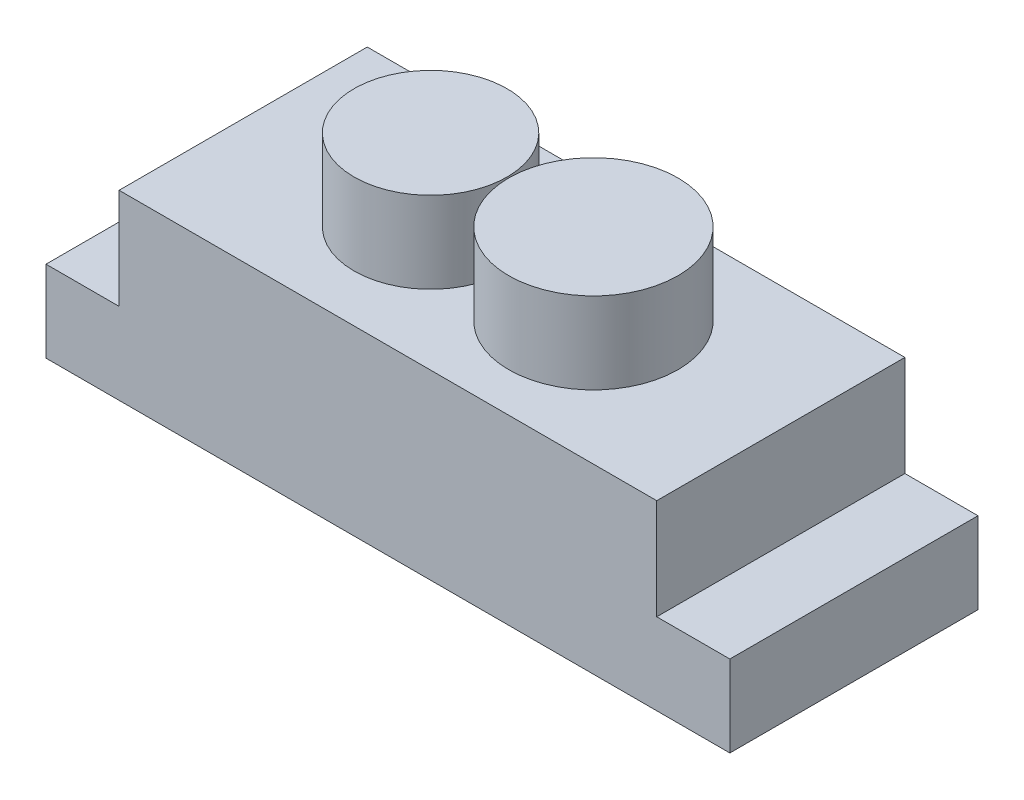
SolidWorks part; units mm, degrees
ref_plane "Front Plane" through (0, 0, 0) normal (0, 0, 1) x (1, 0, 0)
ref_plane "Top Plane" through (0, 0, 0) normal (0, 1, 0) x (1, 0, 0)
ref_plane "Right Plane" through (0, 0, 0) normal (1, 0, 0) x (0, 0, -1)
sketch "Sketch1" plane through (0, 0, 0) normal (0, 1, 0) x (1, 0, 0)
  line L1 (16.51, -7.62) -> (-16.51, -7.62)
  line L2 (16.51, -7.62) -> (16.51, 7.62)
  line L3 (16.51, 7.62) -> (-16.51, 7.62)
  line L4 (-16.51, -7.62) -> (-16.51, 7.62)
  line L5 (16.51, -7.62) -> (-16.51, 7.62) construction
  line L6 (16.51, 7.62) -> (-16.51, -7.62) construction
  point P0 (0, 0)
  dimension "D1" = 33.02
  dimension "D2" = 15.24
extrude "Boss-Extrude1" add sketch "Sketch1" along normal blind 11.176
sketch "Sketch2" plane through (0, 11.176, 0) normal (0, 1, 0) x (1, 0, 0)
  line L0 (-5, 0) -> (5, 0) construction
  circle A0 centre (-5, 0) radius 4.7
  circle A1 centre (5, 0) radius 5.2
  point P4 (0, 0)
  point P5 (-9.7, 0)
  point P7 (10.2, 0)
  point P8 (0, 0)
  dimension "D2" = 9.4
  dimension "D3" = 10.4
  dimension "D1" = 10
extrude "Boss-Extrude2" add sketch "Sketch2" along normal blind 5
sketch "Sketch3" plane through (0, 0, 0) normal (0, -1, 0) x (1, 0, 0)
  line L0 (-16.51, 7.62) -> (16.51, 7.62) construction
  line L1 (21, -7.62) -> (-21, -7.62)
  line L2 (21, -7.62) -> (21, 7.62)
  line L3 (21, 7.62) -> (-21, 7.62)
  line L4 (-21, -7.62) -> (-21, 7.62)
  line L5 (21, -7.62) -> (-21, 7.62) construction
  line L6 (21, 7.62) -> (-21, -7.62) construction
  point P0 (0, 0)
  dimension "D1" = 42
extrude "Boss-Extrude3" add sketch "Sketch3" against normal blind 5
